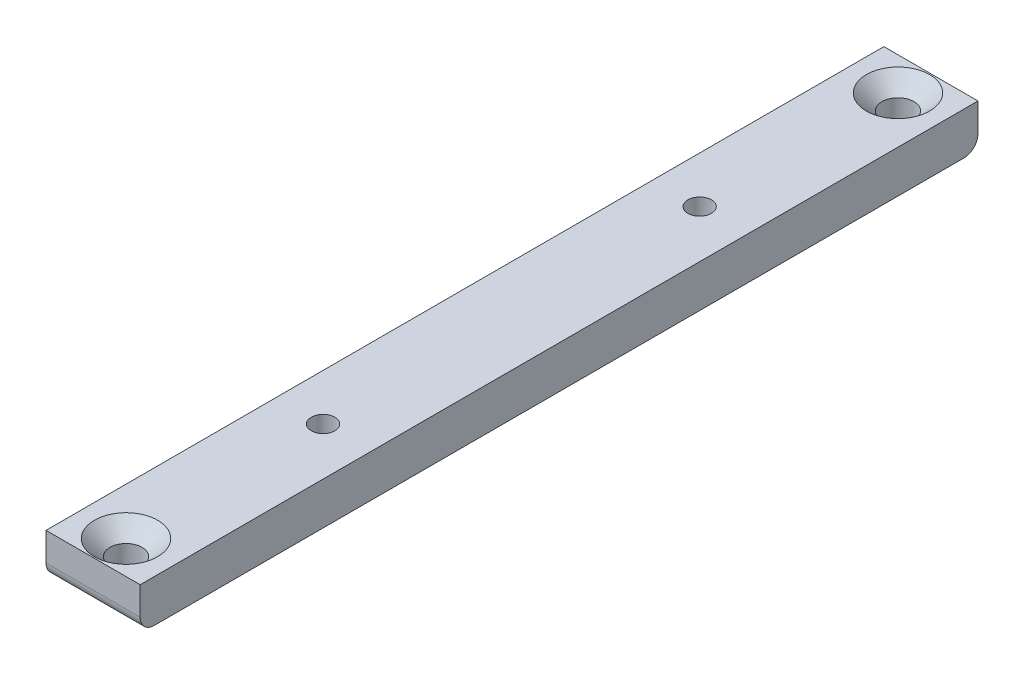
SolidWorks part; units mm, degrees
material "7050-T73510"
ref_plane "Front Plane" through (0, 0, 0) normal (0, 0, 1) x (1, 0, 0)
ref_plane "Top Plane" through (0, 0, 0) normal (0, 1, 0) x (1, 0, 0)
ref_plane "Right Plane" through (0, 0, 0) normal (1, 0, 0) x (0, 0, -1)
sketch "Sketch1" plane through (0, 0, 0) normal (1, 0, 0) x (0, 0, -1)
  line L0 (0, 0) -> (89, 0)
  line L1 (89, 0) -> (89, -4.5)
  line L2 (89, -4.5) -> (0, -4.5)
  line L3 (0, -4.5) -> (0, 0)
  dimension "D1" = 89
  dimension "D2" = 4.5
extrude "Boss-Extrude1" add sketch "Sketch1" along normal blind 10
fillet "Fillet1" radius 1.5 2 edges at (5, -4.5, -89) (5, -4.5, 0)
hole_wizard "CSK for M3 Hex Socket Countersunk Cap Screw1" positions "Sketch3" profile "Sketch2" countersink size "M3" standard "ISO" end condition through all
sketch "Sketch3" plane through (0, 0, 0) normal (0, 1, 0) x (1, 0, 0)
  line L0 (10, 89) -> (10, 0) construction
  line L1 (10, 0) -> (0, 0) construction
  line L2 (10, 89) -> (0, 89) construction
  point P0 (5, 3.5)
  point P2 (5, 85.5)
  point P12 (5, 0)
  dimension "D1" = 5
  dimension "D2" = 3.5
  dimension "D3" = 3.5
sketch "Sketch2" plane through (5, 0, -3.5) normal (1, 0, 0) x (0, 0, 1)
  line L0 (0, 0) -> (0, 4.5)
  line L1 (0, 4.5) -> (1.7, 4.5)
  line L2 (1.7, 4.5) -> (1.7, 1.66)
  line L3 (1.7, 1.66) -> (3.36, 0)
  line L5 (3.36, 0) -> (0, 0)
  line L6 (-1.7, 1.66) -> (-3.36, 0) construction
  line L11 (0, -6.35) -> (0, 107.95) construction
  dimension "Thru Hole Dia." = 3.4
  dimension "Thru Hole Depth" = 4.5
  dimension "Near C'Sink Dia." = 6.72
  dimension "Near C'Sink Angle" = 90
hole_wizard "M3 Tapped Hole1" positions "Sketch5" profile "Sketch4" tap size "M3" standard "ISO"
sketch "Sketch5" plane through (0, 0, 0) normal (0, 1, 0) x (1, 0, 0)
  line L0 (10, 89) -> (0, 89) construction
  point P0 (4.9337, 24.5)
  point P2 (4.9337, 64.5)
  dimension "D1" = 40
  dimension "D2" = 24.5
sketch "Sketch4" plane through (4.9337, 0, -24.5) normal (1, 0, 0) x (0, 0, 1)
  line L0 (0, 0) -> (0, 8.2511)
  line L1 (0, 8.2511) -> (1.25, 7.5)
  line L2 (1.25, 7.5) -> (1.25, 0)
  line L5 (1.25, 0) -> (0, 0)
  line L10 (0, 8.2511) -> (-1.25, 7.5) construction
  line L11 (0, -6.35) -> (0, 107.95) construction
  dimension "Tap Drill Dia." = 2.5
  dimension "Tap Drill Depth" = 7.5
  dimension "Drill Angle" = 118
cosmetic thread "Hole Thread1" parameters "D1"=4.5, "D2"=3
cosmetic thread "Hole Thread2" parameters "D1"=4.5, "D2"=3
